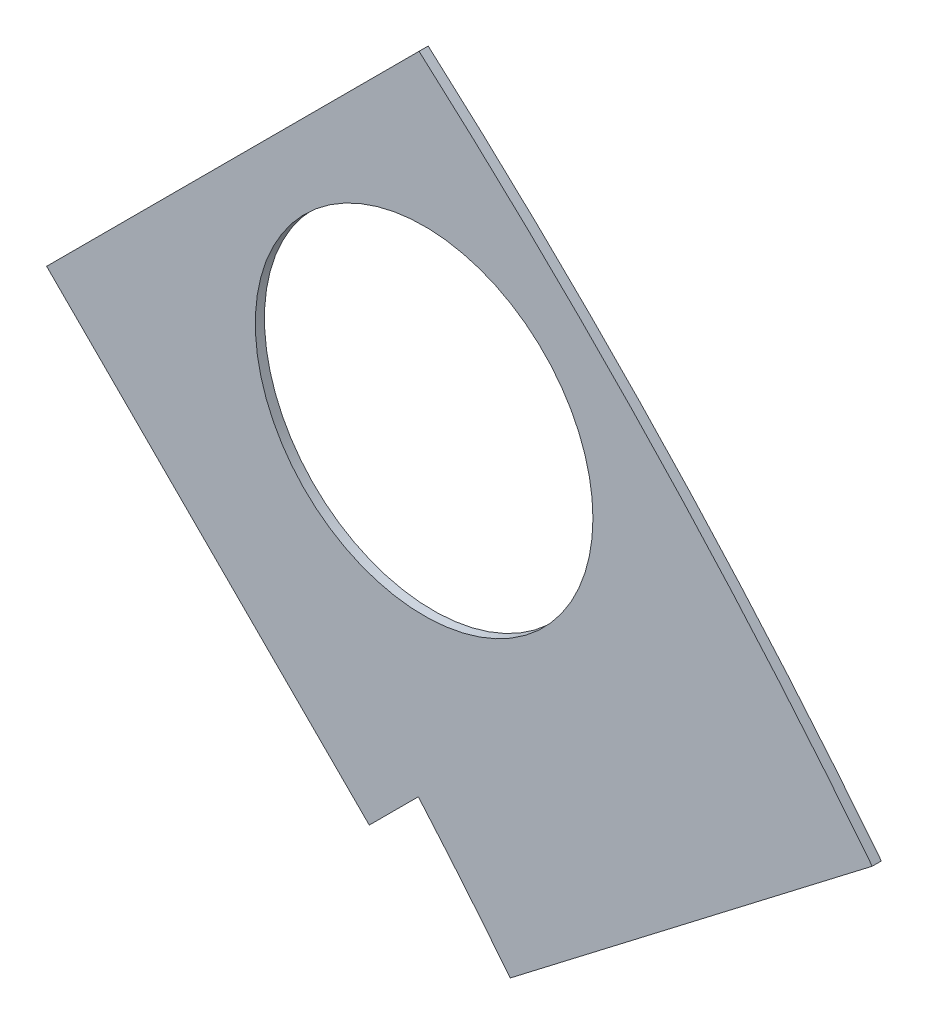
SolidWorks part; units mm, degrees
material "Copper"
ref_plane "Front Plane" through (0, 0, 0) normal (0, 0, 1) x (1, 0, 0)
ref_plane "Top Plane" through (0, 0, 0) normal (0, 1, 0) x (1, 0, 0)
ref_plane "Right Plane" through (0, 0, 0) normal (1, 0, 0) x (0, 0, -1)
sketch "Sketch1" plane through (0, 0, 0) normal (0, 0, 1) x (1, 0, 0)
  line L0 (0, 0) -> (320.3893, 0) construction
  line L1 (0, 0) -> (155.5285, 155.5285) construction
  line L2 (67.2115, 76.1917) -> (8.6967, 17.6769)
  line L3 (8.6967, 17.6769) -> (7.229, 14.1336)
  line L4 (101.4014, -6.35) -> (18.6489, -6.35)
  line L5 (15.1056, -4.8823) -> (18.6489, -6.35)
  line L6 (88.6729, 6.35) -> (27.8605, 6.35)
  line L9 (67.1914, 58.2111) -> (24.1905, 15.2102)
  line L10 (0, 0) -> (40.4486, 97.6516) construction
  line L11 (0, 0) -> (123.4567, -51.1374) construction
  line L18 (8.6967, 17.6769) -> (13.294, 8.6183) construction
  line L19 (18.6489, -6.35) -> (15.4943, 3.3063) construction
  line L20 (27.8605, 6.35) -> (27.7442, 6.7059) construction
  line L21 (24.1905, 15.2102) -> (24.3599, 14.8764) construction
  arc A0 (7.229, 14.1336) -> (15.1056, -4.8823) centre (0, 0) cw
  arc A1 (67.2115, 76.1917) -> (101.4014, -6.35) centre (0, 0) cw
  arc A2 (24.1905, 15.2102) -> (27.8605, 6.35) centre (0, 0) cw
  arc A3 (67.1914, 58.2111) -> (88.6729, 6.35) centre (0, 0) cw
  arc A8 (13.294, 8.6183) -> (15.4943, 3.3063) centre (0, 0) cw construction
  arc A9 (24.3599, 14.8764) -> (27.7442, 6.7059) centre (0, 0) cw construction
  dimension "D1" = 45
  dimension "D3" = 6.35
  dimension "D4" = 15.875
  dimension "D7" = 22.5
  dimension "D8" = 101.6
  dimension "D11" = 12.7
  dimension "D12" = 12.7
  dimension "D2" = 6.35
  dimension "D5" = 67.5
  dimension "D9" = 1.27
  dimension "D10" = 1.27
  dimension "D6" = 12.7
extrude "Boss-Extrude1" add sketch "Sketch1" along normal blind 0.254
sketch "Sketch2" plane through (0, 0, 0.254) normal (0, 0, 1) x (1, 0, 0)
  line L0 (0, 0) -> (101.6, 0) construction
  line L1 (0, 0) -> (71.842, 71.842) construction
  line L3 (0, 0) -> (22.225, 0) construction
  line L4 (0, 0) -> (15.7154, 15.7154) construction
  line L5 (0, 0) -> (95.25, 0) construction
  line L6 (0, 0) -> (92.0044, 24.6525) construction
  arc A0 (101.4014, -6.35) -> (67.2115, 76.1917) centre (0, 0) ccw construction
  circle A1 centre (22.225, 0) radius 4.699
  arc A2 (15.1056, -4.8823) -> (7.229, 14.1336) centre (0, 0) ccw construction
  circle A3 centre (36.195, 0) radius 4.699
  circle A4 centre (61.722, 0) radius 4.699
  circle A5 centre (75.692, 0) radius 4.699
  circle A6 centre (95.25, 0) radius 4.699
  circle A7 centre (15.7154, 15.7154) radius 4.699
  circle A8 centre (25.5937, 25.5937) radius 4.699
  circle A9 centre (43.644, 43.644) radius 4.699
  circle A10 centre (53.5223, 53.5223) radius 4.699
  circle A11 centre (92.0044, 24.6525) radius 4.699
  circle A12 centre (82.4889, 47.625) radius 4.699
  circle A13 centre (67.3519, 67.3519) radius 4.699
  dimension "D3" = 9.398
  dimension "D1" = 45
  dimension "D2" = 6.35
  dimension "D4" = 6.35
  dimension "D5" = 13.97
  dimension "D7" = 13.97
  dimension "D8" = 19.558
  dimension "D9" = 45
  dimension "D10" = 15
  dimension "D11" = 25.527
  dimension "D6" = 2
extrude "Cut-Extrude1" cut sketch "Sketch2" against normal through all
sketch "Sketch3" plane through (0, 0, 0.254) normal (0, 0, 1) x (1, 0, 0)
  line L0 (15.2664, 24.2467) -> (17.0625, 26.0427)
  line L1 (15.2664, 24.2467) -> (15.7154, 23.7977)
  line L2 (17.0625, 26.0427) -> (17.5115, 25.5937)
  line L3 (15.7154, 23.7977) -> (17.5115, 25.5937)
  line L4 (67.2115, 76.1917) -> (8.6967, 17.6769) construction
  line L5 (44.9911, 53.9713) -> (43.195, 52.1753)
  line L6 (44.9911, 53.9713) -> (45.4401, 53.5223)
  line L7 (43.195, 52.1753) -> (43.644, 51.7263)
  line L8 (45.4401, 53.5223) -> (43.644, 51.7263)
  line L9 (27.94, -6.35) -> (30.48, -6.35)
  line L10 (27.94, -6.35) -> (27.94, -5.715)
  line L11 (30.48, -6.35) -> (30.48, -5.715)
  line L12 (27.94, -5.715) -> (30.48, -5.715)
  line L13 (18.6489, -6.35) -> (101.4014, -6.35) construction
  line L14 (67.437, -6.35) -> (69.977, -6.35)
  line L15 (67.437, -6.35) -> (67.437, -5.715)
  line L16 (69.977, -6.35) -> (69.977, -5.715)
  line L17 (67.437, -5.715) -> (69.977, -5.715)
  line L18 (29.2307, 38.211) -> (31.0268, 40.007)
  line L19 (29.2307, 38.211) -> (29.6797, 37.762)
  line L20 (31.0268, 40.007) -> (31.4758, 39.558)
  line L21 (29.6797, 37.762) -> (31.4758, 39.558)
  line L22 (56.845, 65.8253) -> (55.049, 64.0292)
  line L23 (56.845, 65.8253) -> (57.294, 65.3763)
  line L24 (55.049, 64.0292) -> (55.498, 63.5802)
  line L25 (57.294, 65.3763) -> (55.498, 63.5802)
  line L26 (47.6885, -6.35) -> (50.2285, -6.35)
  line L27 (47.6885, -6.35) -> (47.6885, -5.715)
  line L28 (50.2285, -6.35) -> (50.2285, -5.715)
  line L29 (47.6885, -5.715) -> (50.2285, -5.715)
  line L30 (84.201, -6.35) -> (86.741, -6.35)
  line L31 (84.201, -6.35) -> (84.201, -5.715)
  line L32 (86.741, -6.35) -> (86.741, -5.715)
  line L33 (84.201, -5.715) -> (86.741, -5.715)
  line L34 (0, 0) -> (100.7308, 13.2615) construction
  line L35 (0, 0) -> (93.8662, 38.8806) construction
  line L36 (0, 0) -> (80.6047, 61.8502) construction
  line L37 (0, 0) -> (101.6, 0) construction
  line L38 (99.9355, 14.4377) -> (100.267, 11.9194)
  line L39 (99.9355, 14.4377) -> (101.1946, 14.6035)
  line L40 (100.267, 11.9194) -> (101.5261, 12.0852)
  line L41 (101.1946, 14.6035) -> (101.5261, 12.0852)
  line L42 (99.9355, 14.4377) -> (101.5261, 12.0852) construction
  line L43 (100.267, 11.9194) -> (101.1946, 14.6035) construction
  line L44 (93.7655, 37.4643) -> (94.9388, 37.9503)
  line L45 (93.7655, 37.4643) -> (92.7935, 39.811)
  line L46 (94.9388, 37.9503) -> (93.9668, 40.297)
  line L47 (92.7935, 39.811) -> (93.9668, 40.297)
  line L48 (93.7655, 37.4643) -> (93.9668, 40.297) construction
  line L49 (94.9388, 37.9503) -> (92.7935, 39.811) construction
  line L50 (79.3278, 62.4712) -> (80.874, 60.456)
  line L51 (79.3278, 62.4712) -> (80.3354, 63.2443)
  line L52 (80.874, 60.456) -> (81.8816, 61.2292)
  line L53 (80.3354, 63.2443) -> (81.8816, 61.2292)
  line L54 (79.3278, 62.4712) -> (81.8816, 61.2292) construction
  line L55 (80.874, 60.456) -> (80.3354, 63.2443) construction
  line L56 (13.5939, 7.0054) -> (14.5659, 4.6588)
  line L57 (13.5939, 7.0054) -> (14.7672, 7.4914)
  line L58 (14.5659, 4.6588) -> (15.7393, 5.1448)
  line L59 (14.7672, 7.4914) -> (15.7393, 5.1448)
  line L60 (13.5939, 7.0054) -> (15.7393, 5.1448) construction
  line L61 (14.5659, 4.6588) -> (14.7672, 7.4914) construction
  circle A0 centre (15.7154, 15.7154) radius 4.699 construction
  circle A1 centre (43.644, 43.644) radius 4.699 construction
  circle A2 centre (22.225, 0) radius 4.699 construction
  circle A3 centre (61.722, 0) radius 4.699 construction
  arc A4 (101.4014, -6.35) -> (67.2115, 76.1917) centre (0, 0) ccw construction
  arc A9 (15.1056, -4.8823) -> (7.229, 14.1336) centre (0, 0) ccw construction
  circle A10 centre (36.195, 0) radius 4.699 construction
  circle A11 centre (75.692, 0) radius 4.699 construction
  circle A12 centre (25.5937, 25.5937) radius 4.699 construction
  circle A13 centre (53.5223, 53.5223) radius 4.699 construction
  point P75 (14.6666, 6.0751)
  dimension "D2" = 5.715
  dimension "D3" = 2.54
  dimension "D6" = 5.715
  dimension "D8" = 0.635
  dimension "D9" = 5.715
  dimension "D12" = 5.715
  dimension "D4" = 7.5
  dimension "D5" = 22.5
  dimension "D7" = 37.5
  dimension "D10" = 90
  dimension "D11" = 1.27
  dimension "D14" = 0.635
  dimension "D15" = 90
  dimension "D18" = 0.635
  dimension "D19" = 90
  dimension "D22" = 0.635
  dimension "D20" = 1.27
  dimension "D17" = 0.635
  dimension "D13" = 11.4935
  dimension "D16" = 8.509
  dimension "D21" = 11.4935
  dimension "D23" = 8.509
extrude "Cut-Extrude2" cut sketch "Sketch3" against normal through all
sketch "Sketch5" plane through (0, 0, 0.254) normal (0, 0, 1) x (1, 0, 0)
  line L1 (55.947, 66.7233) -> (68.5043, 54.166)
  line L2 (68.5043, 54.166) -> (81.4107, 64.0694)
  line L4 (81.4107, 64.0694) -> (67.3519, 78.1282)
  line L5 (67.3519, 78.1282) -> (55.947, 66.7233)
  line L6 (80.874, 60.456) -> (81.3715, 60.8378) construction
  line L9 (55.049, 64.0292) -> (55.498, 63.5802) construction
  line L10 (67.2115, 76.1917) -> (56.845, 65.8253) construction
  arc A0 (79.8253, 62.8529) -> (67.2115, 76.1917) centre (0, 0) ccw construction
  dimension "D1" = 2.54
  dimension "D2" = 2.54
  dimension "D3" = 1.27
  dimension "D4" = 1.27
extrude "Cut-Extrude5" cut sketch "Sketch5" against normal through all flip side to cut
equation "\"cSep\"= 1.005"
equation "\"D11@Sketch2\"=\"cSep\""
equation "\"cSep2\"= \"D8@Sketch2\""
equation "\"D13@Sketch3\"=\"cSep\"/2-.05"
equation "\"D16@Sketch3\"=\"cSep2\"/2-.05"
equation "\"D21@Sketch3\"=\"cSep\"/2-.05"
equation "\"D23@Sketch3\"=\"cSep2\"/2-.05"
